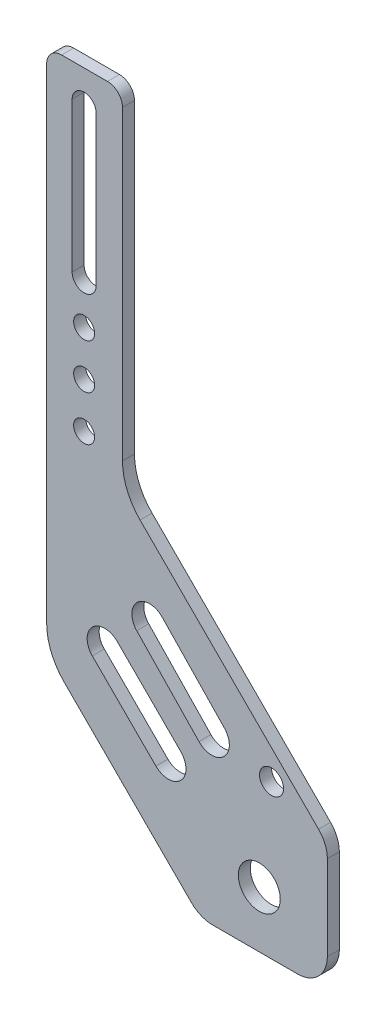
SolidWorks part; units mm, degrees
ref_plane "Front Plane" through (0, 0, 0) normal (0, 0, 1) x (1, 0, 0)
ref_plane "Top Plane" through (0, 0, 0) normal (0, 1, 0) x (1, 0, 0)
ref_plane "Right Plane" through (0, 0, 0) normal (1, 0, 0) x (0, 0, -1)
sketch "Sketch1" plane through (0, 0, 0) normal (0, 0, 1) x (1, 0, 0)
  line L0 (12.5, 119) -> (12.5, 69) construction
  line L2 (0, 5) -> (0, 125)
  line L3 (5, 130) -> (20.3018, 130)
  line L4 (25.3018, 22.8352) -> (25.3018, 125)
  line L5 (16.5, 119) -> (16.5, 69)
  line L6 (8.5, 119) -> (8.5, 69)
  line L7 (5.8579, -50.8579) -> (48.3088, -93.3088)
  line L8 (0, 5) -> (0, -36.7157)
  line L9 (90.7352, -50.8824) -> (31.1597, 8.6931)
  line L10 (57.6713, -17.8185) -> (90.7352, -50.8824)
  line L11 (60, 5) -> (60, -20.1472) construction
  line L12 (60, -20.1472) -> (93.6642, -53.8113) construction
  line L13 (0, 5) -> (0, -45) construction
  line L14 (0, -45) -> (51.2377, -96.2377) construction
  line L15 (19.3934, -34.3934) -> (40.6066, -55.6066) construction
  line L16 (23.5536, -30.2332) -> (44.7668, -51.4464)
  line L17 (15.2332, -38.5536) -> (36.4464, -59.7668)
  line L18 (34.1602, -40.8398) -> (57.6713, -17.8185) construction
  line L19 (55.3799, -96.2377) -> (83.6642, -96.2377)
  line L20 (34.3089, -19.7886) -> (55.0709, -41.4437) construction
  line L21 (30.0621, -23.8603) -> (50.824, -45.5154)
  line L22 (38.5557, -15.717) -> (59.3177, -37.372)
  line L23 (93.6642, -86.2377) -> (93.6642, -57.9535)
  arc A2 (20.3018, 130) -> (25.3018, 125) centre (20.3018, 125) cw
  arc A3 (5, 130) -> (0, 125) centre (5, 125) ccw
  arc A4 (16.5, 119) -> (8.5, 119) centre (12.5, 119) ccw
  arc A5 (8.5, 69) -> (16.5, 69) centre (12.5, 69) ccw
  circle A6 centre (12.5, 55) radius 3.5
  circle A7 centre (12.5, 40) radius 3.5
  circle A8 centre (12.5, 25) radius 3.5
  arc A9 (31.1597, 8.6931) -> (25.3018, 22.8352) centre (45.3018, 22.8352) cw
  arc A10 (0, -36.7157) -> (5.8579, -50.8579) centre (20, -36.7157) ccw
  arc A11 (23.5536, -30.2332) -> (15.2332, -38.5536) centre (19.3934, -34.3934) ccw
  arc A12 (36.4464, -59.7668) -> (44.7668, -51.4464) centre (40.6066, -55.6066) ccw
  arc A13 (30.0621, -23.8603) -> (38.5557, -15.717) centre (34.3089, -19.7886) cw
  arc A14 (59.3177, -37.372) -> (50.824, -45.5154) centre (55.0709, -41.4437) cw
  circle A15 centre (70.9538, -77.5131) radius 7
  circle A16 centre (75.0383, -45) radius 4
  arc A17 (93.6642, -57.9535) -> (90.7352, -50.8824) centre (83.6642, -57.9535) ccw
  arc A18 (48.3088, -93.3088) -> (55.3799, -96.2377) centre (55.3799, -86.2377) ccw
  arc A19 (83.6642, -96.2377) -> (93.6642, -86.2377) centre (83.6642, -86.2377) ccw
  point P5 (30, -45)
  point P7 (0, 0)
  point P16 (12.5, 94)
  point P46 (44.6899, -30.6162)
  point P54 (0, 0)
  dimension "D1" = 10
  dimension "D2" = 20
  dimension "D3" = 3
  dimension "D4" = 60
extrude "Boss-Extrude1" add sketch "Sketch1" along normal blind 4 contours L19 A19 L23 A17 L9 A9 L4 A2 L3 A3 L2 L8 A10 L7 A18 L22 A14 L21 A13 A5 L6 A4 L5 A6 A7 A8 A12 L17 A11 L16 A15 A16
